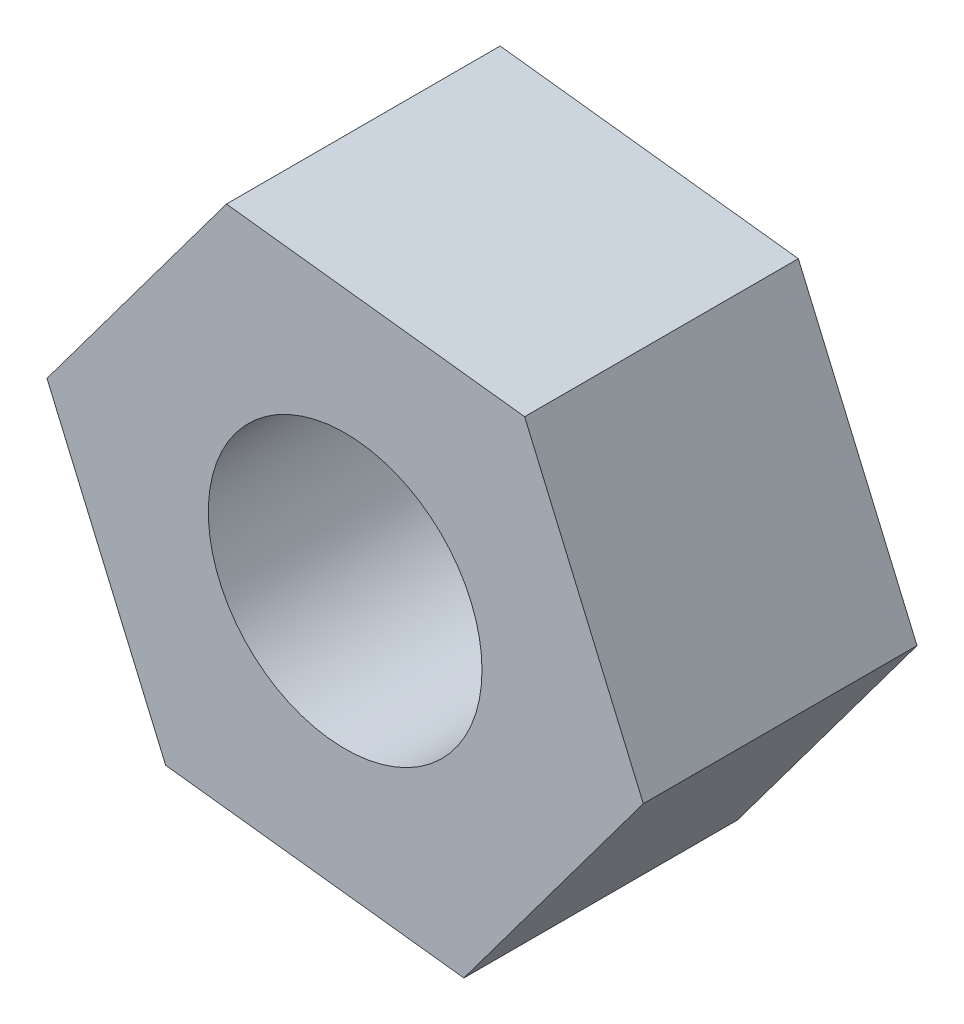
SolidWorks part; units mm, degrees
material "尼龙 6/10"
ref_plane "前视基准面" through (0, 0, 0) normal (0, 0, 1) x (1, 0, 0)
ref_plane "上视基准面" through (0, 0, 0) normal (0, 1, 0) x (1, 0, 0)
ref_plane "右视基准面" through (0, 0, 0) normal (1, 0, 0) x (0, 0, -1)
other "Configuration Table"
sketch "草图1" plane through (0, 0, 0) normal (0, 0, 1) x (1, 0, 0)
  line L1 (-18.8187, -18.7327) -> (-20.9976, -18.4764)
  line L2 (-20.9976, -18.4764) -> (-22.309, -20.2352)
  line L3 (-22.309, -20.2352) -> (-21.4416, -22.2504)
  line L4 (-21.4416, -22.2504) -> (-19.2627, -22.5067)
  line L5 (-19.2627, -22.5067) -> (-17.9512, -20.7479)
  line L6 (-17.9512, -20.7479) -> (-18.8187, -18.7327)
  circle A0 centre (-20.1301, -20.4915) radius 1.9 construction
  circle A1 centre (-20.1301, -20.4915) radius 1
  dimension "D2" = 2
  dimension "D1" = 3.8
extrude "凸台-拉伸1" add sketch "草图1" along normal blind 2
